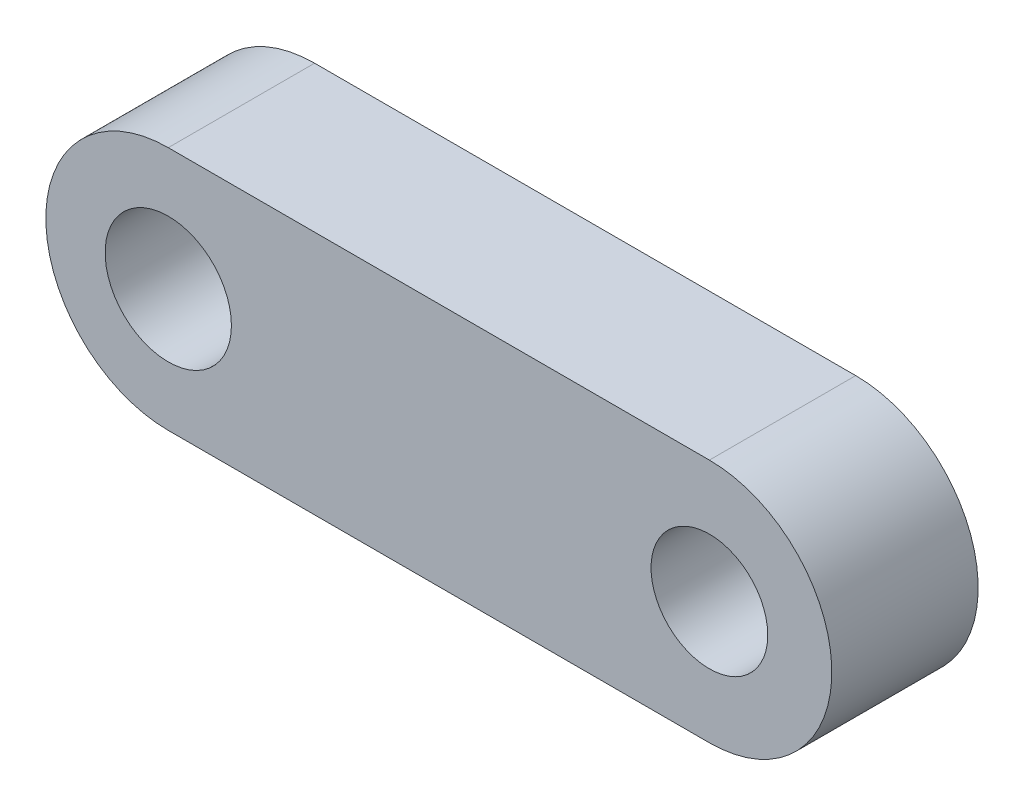
SolidWorks part; units mm, degrees
ref_plane "Front Plane" through (0, 0, 0) normal (0, 0, 1) x (1, 0, 0)
ref_plane "Top Plane" through (0, 0, 0) normal (0, 1, 0) x (1, 0, 0)
ref_plane "Right Plane" through (0, 0, 0) normal (1, 0, 0) x (0, 0, -1)
sketch "Sketch1" plane through (0, 0, 0) normal (0, 0, 1) x (1, 0, 0)
  line L0 (-61.0175, 27.6105) -> (61.0175, 27.6105)
  line L1 (61.0175, -27.6105) -> (-61.0175, -27.6105)
  arc A0 (-61.0175, 27.6105) -> (-61.0175, -27.6105) centre (-61.0175, 0) ccw
  arc A1 (61.0175, 27.6105) -> (61.0175, -27.6105) centre (61.0175, 0) cw
  circle A2 centre (-61.0175, 0) radius 14.2383
  circle A3 centre (61.0175, 0) radius 13.159
extrude "Boss-Extrude1" add sketch "Sketch1" along normal blind 33
ref_plane "Plane1" through (0, 0, 16.5) normal (0, 0, 1) x (1, 0, 0)
